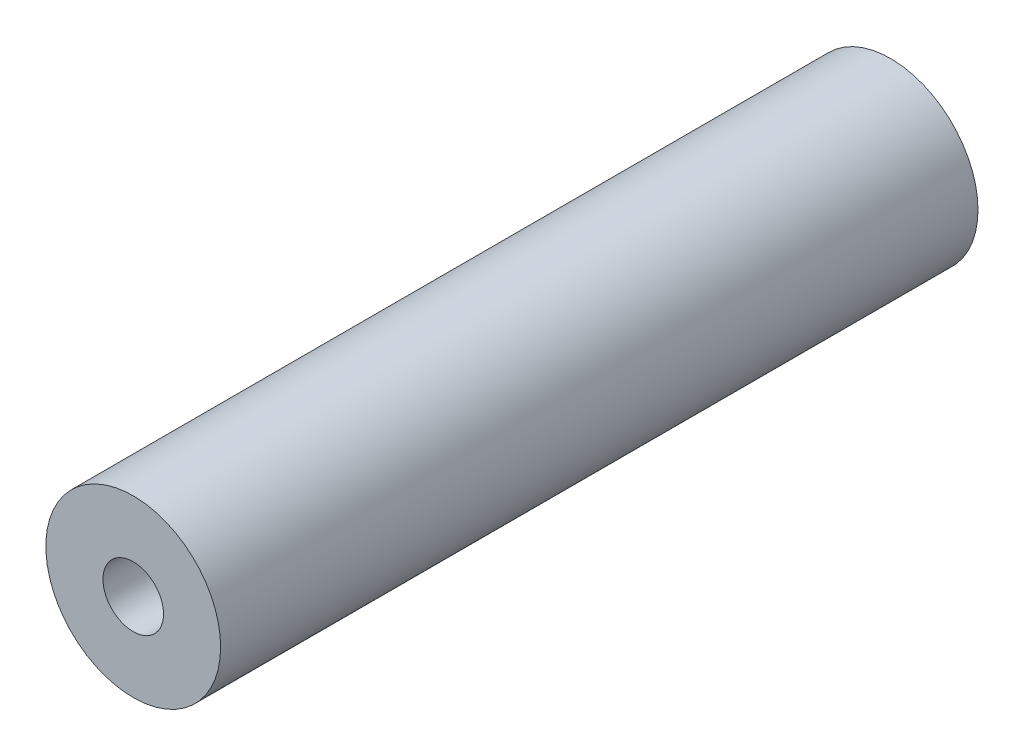
SolidWorks part; units mm, degrees
ref_plane "Front Plane" through (0, 0, 0) normal (0, 0, 1) x (1, 0, 0)
ref_plane "Top Plane" through (0, 0, 0) normal (0, 1, 0) x (1, 0, 0)
ref_plane "Right Plane" through (0, 0, 0) normal (1, 0, 0) x (0, 0, -1)
sketch "Sketch1" plane through (0, 0, 0) normal (0, 0, 1) x (1, 0, 0)
  circle A0 centre (0, 0) radius 4.7625
  dimension "D2" = 9.525
extrude "Boss-Extrude1" add sketch "Sketch1" along normal blind 41.275
hole_wizard "M4x0.7 Tapped Hole1" positions "Sketch2" profile "Sketch3" tap size "M4x0.7" standard "ANSI Metric"
sketch "Sketch2" plane through (0, 0, 41.275) normal (0, 0, 1) x (1, 0, 0)
  point P0 (0, 0)
sketch "Sketch3" plane through (0, 0, 41.275) normal (1, 0, 0) x (0, -1, 0)
  line L0 (0, 0) -> (0, 13.6914)
  line L1 (0, 13.6914) -> (1.65, 12.7)
  line L2 (1.65, 12.7) -> (1.65, 0)
  line L5 (1.65, 0) -> (0, 0)
  line L10 (0, 13.6914) -> (-1.65, 12.7) construction
  line L11 (0, -6.35) -> (0, 107.95) construction
  dimension "Tap Drill Dia." = 3.3
  dimension "Tap Drill Depth" = 12.7
  dimension "Drill Angle" = 118
cosmetic thread "Hole Thread1"
hole_wizard "#8-32 Tapped Hole1" positions "Sketch4" profile "Sketch5" tap size "#8-32" standard "ANSI Inch"
sketch "Sketch4" plane through (0, 0, 0) normal (0, 0, -1) x (-1, 0, 0)
  point P0 (0, 0)
sketch "Sketch5" plane through (0, 0, 0) normal (1, 0, 0) x (0, 1, 0)
  line L0 (0, 0) -> (0, 14.2458)
  line L1 (0, 14.2458) -> (1.7272, 13.208)
  line L2 (1.7272, 13.208) -> (1.7272, 0)
  line L5 (1.7272, 0) -> (0, 0)
  line L10 (0, 14.2458) -> (-1.7272, 13.208) construction
  line L11 (0, -6.35) -> (0, 107.95) construction
  dimension "Tap Drill Dia." = 3.4544
  dimension "Tap Drill Depth" = 13.208
  dimension "Drill Angle" = 118
cosmetic thread "Hole Thread2"
